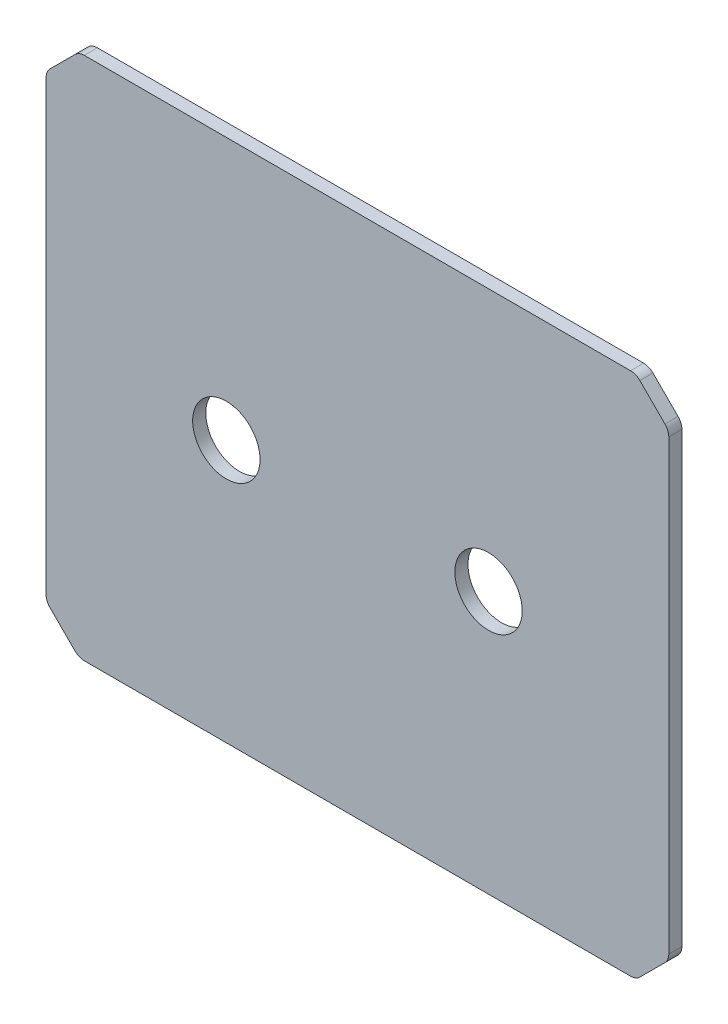
SolidWorks part; units mm, degrees
ref_plane "Front" through (0, 0, 0) normal (0, 0, 1) x (1, 0, 0)
ref_plane "Top" through (0, 0, 0) normal (0, 1, 0) x (1, 0, 0)
ref_plane "Right" through (0, 0, 0) normal (1, 0, 0) x (0, 0, -1)
sketch "Sketch1" plane through (0, 0, 0) normal (0, 0, 1) x (1, 0, 0)
  line L1 (0, 0) -> (60.325, 0)
  line L2 (0, 0) -> (0, 50.8)
  line L3 (0, 50.8) -> (60.325, 50.8)
  line L4 (60.325, 0) -> (60.325, 50.8)
  dimension "D1" = 50.8
  dimension "D2" = 60.325
extrude "Boss-Extrude1" add sketch "Sketch1" along normal blind 1.27 contours L1 L4 L3 L2
sketch "Sketch3" plane through (0, 0, 1.27) normal (0, 0, 1) x (1, 0, 0)
  line L1 (60.325, 0) -> (60.325, 50.8) construction
  line L2 (0, 50.8) -> (60.325, 50.8) construction
  circle A0 centre (17.4625, 25.4) radius 3.2639
  circle A1 centre (42.8625, 25.4) radius 3.2639
  dimension "D1" = 6.5278
  dimension "D2" = 6.5278
  dimension "D3" = 25.4
  dimension "D4" = 17.4625
  dimension "D5" = 25.4
  dimension "D6" = 25.4
extrude "Cut-Extrude1" cut sketch "Sketch3" against normal through all contours A1 | A0
chamfer "Chamfer1" distance 3.175 angle 45 4 edges at (0, 0, 0.635) (0, 50.8, 0.635) (60.325, 50.8, 0.635) (60.325, 0, 0.635)
fillet "Fillet1" radius 1.27 8 edges at (0, 47.625, 0.635) (3.175, 50.8, 0.635) (57.15, 50.8, 0.635) (60.325, 47.625, 0.635) (60.325, 3.175, 0.635) (57.15, 0, 0.635) (3.175, 0, 0.635) (0, 3.175, 0.635)
